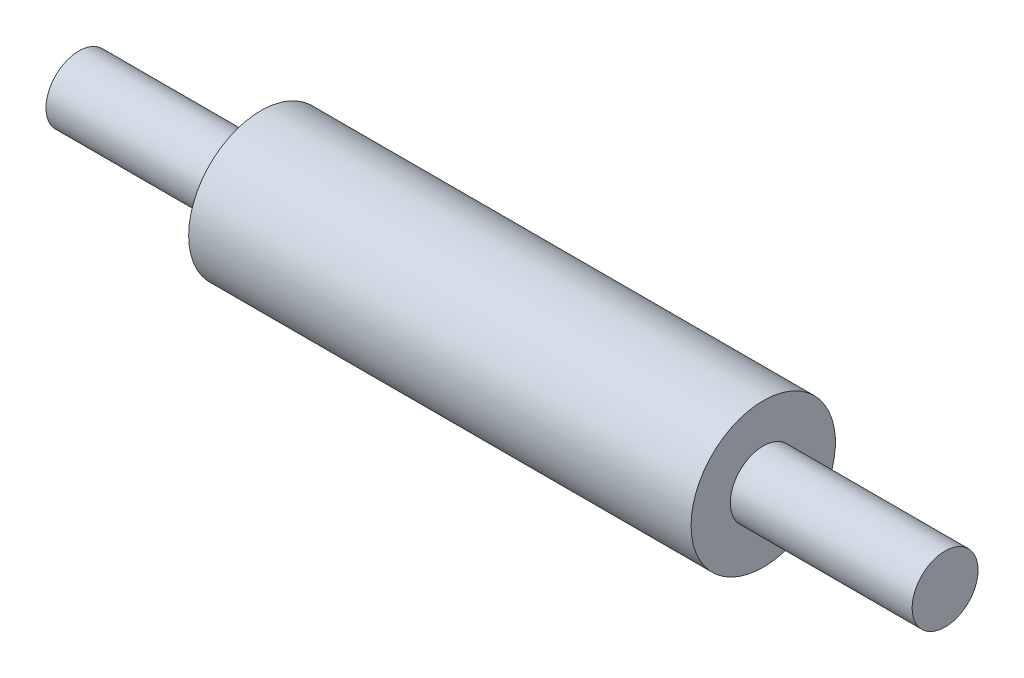
SolidWorks part; units mm, degrees
material "6061-T6 (SS)"
ref_plane "Front Plane" through (0, 0, 0) normal (0, 0, 1) x (1, 0, 0)
ref_plane "Top Plane" through (0, 0, 0) normal (0, 1, 0) x (1, 0, 0)
ref_plane "Right Plane" through (0, 0, 0) normal (1, 0, 0) x (0, 0, -1)
sketch "Sketch1" plane through (0, 0, 0) normal (0, 0, 1) x (1, 0, 0)
  line L0 (-19.4787, 0) -> (21.5534, 0) construction
  line L1 (0, 1.5875) -> (0, 0.725)
  line L2 (0, 1.5875) -> (11.05, 1.5875)
  line L3 (11.05, 1.5875) -> (11.05, 0.725)
  line L4 (11.05, 0.725) -> (15.05, 0.725)
  line L5 (15.05, 0.725) -> (15.05, 0)
  line L6 (0, 0.725) -> (-4, 0.725)
  line L7 (-4, 0.725) -> (-4, 0)
  line L8 (-4, 0) -> (15.05, 0)
  dimension "D1" = 1.45
  dimension "D2" = 3.175
  dimension "D3" = 4
  dimension "D4" = 4
  dimension "D5" = 19.05
revolve "Revolve1" add sketch "Sketch1" angle 360 about L0
